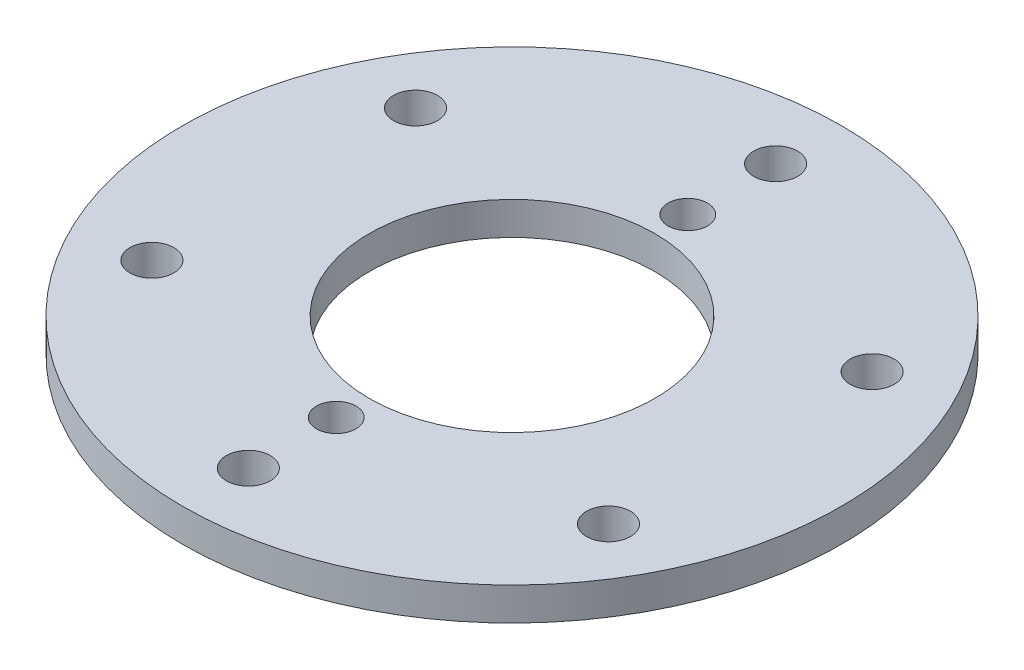
SolidWorks part; units mm, degrees
ref_plane "Front Plane" through (0, 0, 0) normal (0, 0, 1) x (1, 0, 0)
ref_plane "Top Plane" through (0, 0, 0) normal (0, 1, 0) x (1, 0, 0)
ref_plane "Right Plane" through (0, 0, 0) normal (1, 0, 0) x (0, 0, -1)
sketch "Sketch1" plane through (0, 0, 0) normal (0, 1, 0) x (1, 0, 0)
  circle A0 centre (0, 0) radius 150
  circle A1 centre (0, 0) radius 120 construction
  circle A2 centre (0, 0) radius 80 construction
  circle A3 centre (0, 0) radius 65
  circle A4 centre (0, 120) radius 10
  circle A5 centre (0, 80) radius 9
  circle A6 centre (103.923, 60) radius 10
  circle A7 centre (103.923, -60) radius 10
  circle A8 centre (0, -120) radius 10
  circle A9 centre (-103.923, -60) radius 10
  circle A10 centre (-103.923, 60) radius 10
  circle A11 centre (0, -80) radius 9
  point P22 (0, 0)
  point P26 (0, 0)
  dimension "D1" = 300
  dimension "D2" = 130
  dimension "D3" = 240
  dimension "D4" = 160
  dimension "D5" = 20
  dimension "D6" = 18
  dimension "D7" = 6
  dimension "D8" = 2
extrude "Boss-Extrude1" add sketch "Sketch1" along normal blind 15
